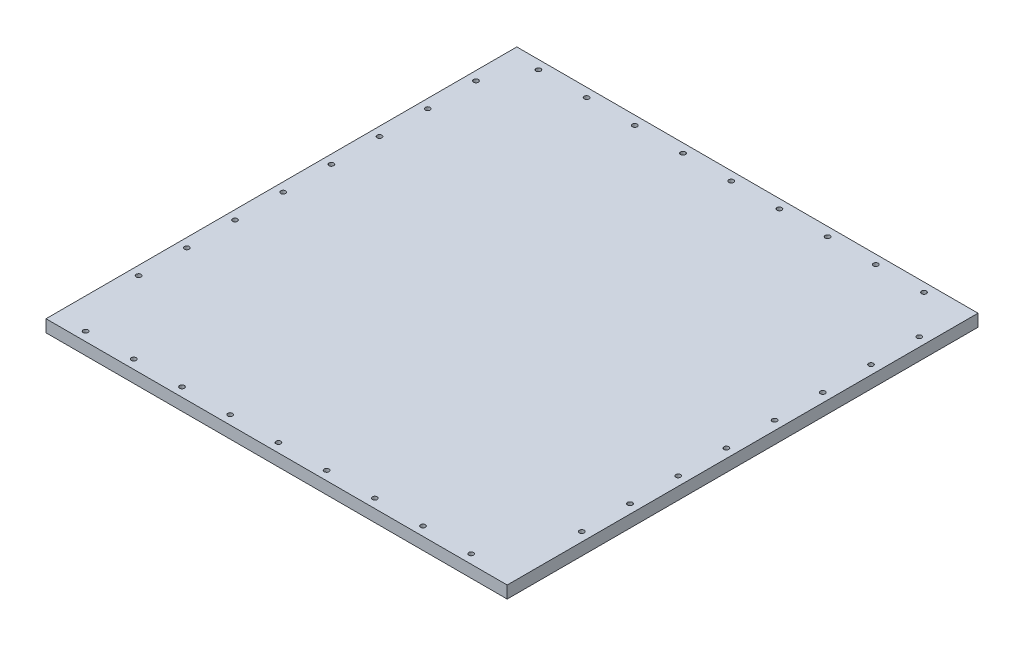
SolidWorks part; units mm, degrees
ref_plane "Front Plane" through (0, 0, 0) normal (0, 0, 1) x (1, 0, 0)
ref_plane "Top Plane" through (0, 0, 0) normal (0, 1, 0) x (1, 0, 0)
ref_plane "Right Plane" through (0, 0, 0) normal (1, 0, 0) x (0, 0, -1)
sketch "Sketch1" plane through (0, 0, 0) normal (0, 1, 0) x (1, 0, 0)
  line L1 (-240, -245) -> (240, -245)
  line L2 (-240, -245) -> (-240, 245)
  line L3 (-240, 245) -> (240, 245)
  line L4 (240, -245) -> (240, 245)
  line L5 (-240, -245) -> (240, 245) construction
  line L6 (-240, 245) -> (240, -245) construction
  point P0 (0, 0)
  dimension "D1" = 480
  dimension "D2" = 490
extrude "Boss-Extrude1" add sketch "Sketch1" along normal blind 12.7
sketch "Sketch3" plane through (0, 12.7, 0) normal (0, 1, 0) x (1, 0, 0)
  line L1 (-240, 245) -> (-220, 245)
  line L2 (-240, 245) -> (-240, 205)
  line L3 (-240, 205) -> (-220, 205)
  line L4 (-220, 245) -> (-220, 205)
  line L7 (240, 245) -> (220, 245)
  line L8 (240, 245) -> (240, 205)
  line L9 (240, 205) -> (220, 205)
  line L10 (220, 245) -> (220, 205)
  line L11 (-240, -245) -> (-220, -245)
  line L12 (-240, -245) -> (-240, -205)
  line L13 (-240, -205) -> (-220, -205)
  line L14 (-220, -245) -> (-220, -205)
  line L15 (240, -245) -> (220, -245)
  line L16 (240, -245) -> (240, -205)
  line L17 (240, -205) -> (220, -205)
  line L18 (220, -245) -> (220, -205)
  dimension "D1" = 20
  dimension "D2" = 40
  dimension "D3" = 40
  dimension "D4" = 20
  dimension "D5" = 40
  dimension "D6" = 20
  dimension "D7" = 20
  dimension "D8" = 40
sketch "Sketch4" plane through (0, 12.7, 0) normal (0, 1, 0) x (1, 0, 0)
  line L0 (240, 245) -> (-240, 245) construction
  line L1 (-220, 245) -> (-220, 205) construction
  circle A0 centre (-208.14, 235.64) radius 2.5
  dimension "D1" = 9.36
  dimension "D2" = 5
  dimension "D3" = 11.86
extrude "Cut-Extrude2" cut sketch "Sketch4" against normal through all both
pattern_linear "LPattern3" count 10 spacing 50.16 along (1, 0, 0) of "Cut-Extrude2"
sketch "Sketch5" plane through (0, 12.7, 0) normal (0, 1, 0) x (1, 0, 0)
  line L0 (-240, 245) -> (-240, -245) construction
  line L1 (-240, 205) -> (-220, 205) construction
  circle A0 centre (-230.64, 193.14) radius 2.5
  dimension "D1" = 5
  dimension "D2" = 9.36
  dimension "D3" = 11.86
extrude "Cut-Extrude3" cut sketch "Sketch5" against normal through all both
pattern_linear "LPattern4" count 8 spacing 50.16 along (0, 0, 1) of "Cut-Extrude3"
sketch "Sketch6" plane through (0, 12.7, 0) normal (0, 1, 0) x (1, 0, 0)
  line L0 (-240, -245) -> (240, -245) construction
  line L1 (-220, -245) -> (-220, -205) construction
  circle A0 centre (-208.14, -235.64) radius 2.5
  dimension "D1" = 5
  dimension "D2" = 9.36
  dimension "D3" = 11.86
extrude "Cut-Extrude4" cut sketch "Sketch6" against normal through all both
pattern_linear "LPattern5" count 10 spacing 50.16 along (1, 0, 0) of "Cut-Extrude4"
sketch "Sketch7" plane through (0, 12.7, 0) normal (0, 1, 0) x (1, 0, 0)
  line L0 (240, -245) -> (240, 245) construction
  line L1 (240, 205) -> (220, 205) construction
  circle A0 centre (230.64, 193.14) radius 2.5
  dimension "D1" = 5
  dimension "D2" = 9.36
  dimension "D3" = 11.86
extrude "Cut-Extrude5" cut sketch "Sketch7" against normal through all both
pattern_linear "LPattern6" count 8 spacing 50.16 along (0, 0, 1) of "Cut-Extrude5"
